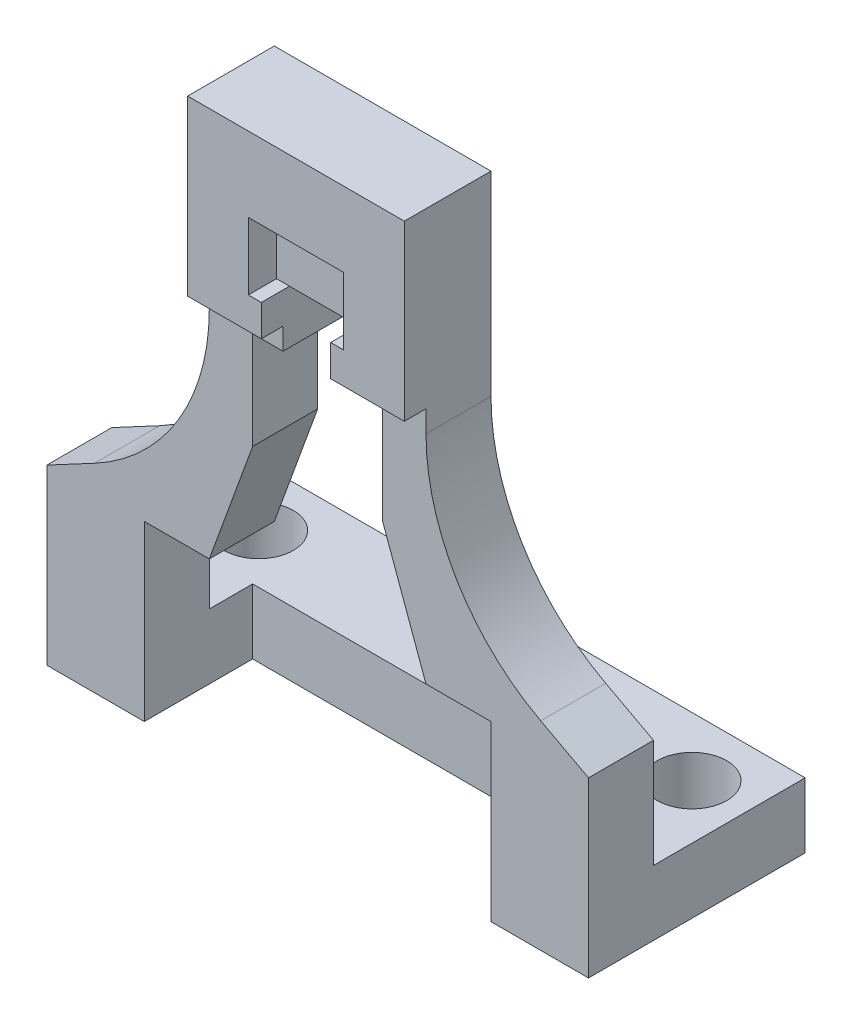
SolidWorks part; units mm, degrees
ref_plane "Спереди" through (0, 0, 0) normal (0, 0, 1) x (1, 0, 0)
ref_plane "Сверху" through (0, 0, 0) normal (0, 1, 0) x (1, 0, 0)
ref_plane "Справа" through (0, 0, 0) normal (1, 0, 0) x (0, 0, -1)
sketch "Sketch7" plane through (0, 0, 0) normal (0, 1, 0) x (1, 0, 0)
  line L0 (-12.5, 2.2767) -> (12.5, 2.2767) construction
  line L1 (12.5, -5) -> (-12.5, -5)
  line L2 (12.5, -5) -> (12.5, 5)
  line L3 (12.5, 5) -> (-12.5, 5)
  line L4 (-12.5, -5) -> (-12.5, 5)
  line L5 (12.5, -5) -> (-12.5, 5) construction
  line L6 (12.5, 5) -> (-12.5, -5) construction
  circle A0 centre (-10, 2.2767) radius 1.6
  circle A1 centre (10, 2.2767) radius 1.6
  point P0 (0, 0)
  dimension "D3" = 3.2
  dimension "D1" = 25
  dimension "D2" = 10
  dimension "D4" = 20
  dimension "D5" = 10
extrude "Boss-Extrude3" add sketch "Sketch7" along normal blind 3
sketch "Sketch8" plane through (0, 3, 0) normal (0, 1, 0) x (1, 0, 0)
  line L1 (12.5, -2) -> (-12.5, -2)
  line L2 (12.5, -2) -> (12.5, -5)
  line L3 (12.5, -5) -> (-12.5, -5)
  line L4 (-12.5, -2) -> (-12.5, -5)
  line L5 (12.5, -2) -> (-12.5, -5) construction
  line L6 (12.5, -5) -> (-12.5, -2) construction
  point P0 (0, -3.5)
  dimension "D1" = 3
extrude "Boss-Extrude4" add sketch "Sketch8" along normal blind 24
sketch "Sketch9" plane through (0, 0, 5) normal (0, 0, 1) x (1, 0, 0)
  line L0 (-12.5, 0) -> (12.5, 0) construction
  line L1 (8, 8) -> (-8, 8) construction
  line L2 (8, 8) -> (8, 0)
  line L3 (8, 0) -> (-8, 0)
  line L4 (-8, 8) -> (-8, 0)
  line L5 (8, 8) -> (-8, 0) construction
  line L6 (8, 0) -> (-8, 8) construction
  line L7 (0, 27) -> (0, 0) construction
  line L8 (-12.5, 27) -> (12.5, 27) construction
  line L9 (-8, 8) -> (-3, 8)
  line L10 (3, 18) -> (-3, 18)
  line L11 (3, 18) -> (3, 8)
  line L12 (3, 8) -> (-3, 8) construction
  line L13 (-3, 18) -> (-3, 8)
  line L14 (3, 18) -> (-3, 8) construction
  line L15 (3, 8) -> (-3, 18) construction
  line L16 (3, 8) -> (8, 8)
  point P0 (0, 4)
  point P13 (0, 13)
  dimension "D1" = 8
  dimension "D2" = 16
  dimension "D3" = 10
  dimension "D4" = 6
extrude "Cut-Extrude5" cut sketch "Sketch9" against normal blind 5
sketch "Sketch10" plane through (0, 0, 5) normal (0, 0, 1) x (1, 0, 0)
  line L0 (0, 27) -> (0, 8) construction
  line L1 (-12.5, 27) -> (12.5, 27) construction
  line L3 (-5, 27) -> (-5, 12)
  line L4 (-3, 8) -> (-8, 8) construction
  line L5 (5, 8) -> (5, 27) construction
  line L6 (5, 27) -> (-5, 27)
  line L7 (-5, 8) -> (-5, 27) construction
  line L8 (5, 8) -> (-5, 27) construction
  line L9 (5, 27) -> (-5, 8) construction
  line L10 (-5, 12) -> (-12.5, 8)
  line L11 (-12.5, 27) -> (-12.5, 0) construction
  line L12 (5, 27) -> (5, 12)
  line L13 (5, 12) -> (12.5, 8)
  line L14 (12.5, 27) -> (12.5, 0) construction
  line L15 (-12.5, 8) -> (12.5, 8) construction
  line L16 (-12.5, 8) -> (-12.5, 0)
  line L17 (-12.5, 0) -> (12.5, 0)
  line L18 (12.5, 0) -> (12.5, 8)
  point P4 (0, 0)
  point P6 (0, 17.5)
  point P11 (0, 0)
  point P24 (0, 0)
  point P27 (0, 0)
  dimension "D1" = 10
  dimension "D2" = 15
extrude "Cut-Extrude6" cut sketch "Sketch10" against normal blind 5 flip side to cut
sketch "Sketch11" plane through (0, 0, 5) normal (0, 0, 1) x (1, 0, 0)
  line L0 (0, 27) -> (0, 0) construction
  line L1 (-5, 27) -> (5, 27) construction
  line L3 (5, 19) -> (-5, 19)
  line L4 (5, 19) -> (5, 27)
  line L5 (5, 27) -> (-5, 27)
  line L6 (-5, 19) -> (-5, 27)
  line L7 (5, 19) -> (-5, 27) construction
  line L8 (5, 27) -> (-5, 19) construction
  point P5 (0, 23)
  dimension "D1" = 8
extrude "Boss-Extrude5" add sketch "Sketch11" along normal blind 1
chamfer "Chamfer1" distance 2 angle 70 2 edges at (3, 8, 3.5) (-3, 8, 3.5)
sketch "Sketch12" plane through (0, 0, 6) normal (0, 0, 1) x (1, 0, 0)
  line L0 (0, 27) -> (0, 19) construction
  line L1 (5, 27) -> (-5, 27) construction
  line L2 (-5, 19) -> (5, 19) construction
  line L3 (-2.2, 20.45) -> (-1.6, 20.45)
  line L4 (2.2, 20.45) -> (-2.2, 20.45) construction
  line L5 (2.2, 20.45) -> (2.2, 23.55)
  line L6 (2.2, 23.55) -> (-2.2, 23.55)
  line L7 (-2.2, 20.45) -> (-2.2, 23.55)
  line L8 (2.2, 20.45) -> (-2.2, 23.55) construction
  line L9 (2.2, 23.55) -> (-2.2, 20.45) construction
  line L10 (-1.6, 20.45) -> (-1.6, 19)
  line L11 (-1.6, 19) -> (1.6, 19)
  line L12 (1.6, 19) -> (1.6, 20.45)
  line L13 (1.6, 20.45) -> (2.2, 20.45)
  point P6 (0, 22)
  dimension "D1" = 3.1
  dimension "D2" = 4.4
  dimension "D3" = 3.2
  dimension "D4" = 3
extrude "Cut-Extrude7" cut sketch "Sketch12" against normal blind 1.3
sketch "Sketch14" plane through (0, 0, 4.7) normal (0, 0, 1) x (1, 0, 0)
  line L0 (-1.6, 20.45) -> (-1.6, 16.6369)
  line L1 (-1.6, 16.6369) -> (1.6, 16.6369)
  line L2 (1.6, 16.6369) -> (1.6, 20.45)
  line L3 (1.6, 20.45) -> (-1.6, 20.45)
extrude "Cut-Extrude9" cut sketch "Sketch14" against normal through all both and the other way through all
fillet "Fillet3" radius 10 2 edges at (5, 12, 3.5) (-5, 12, 3.5)
